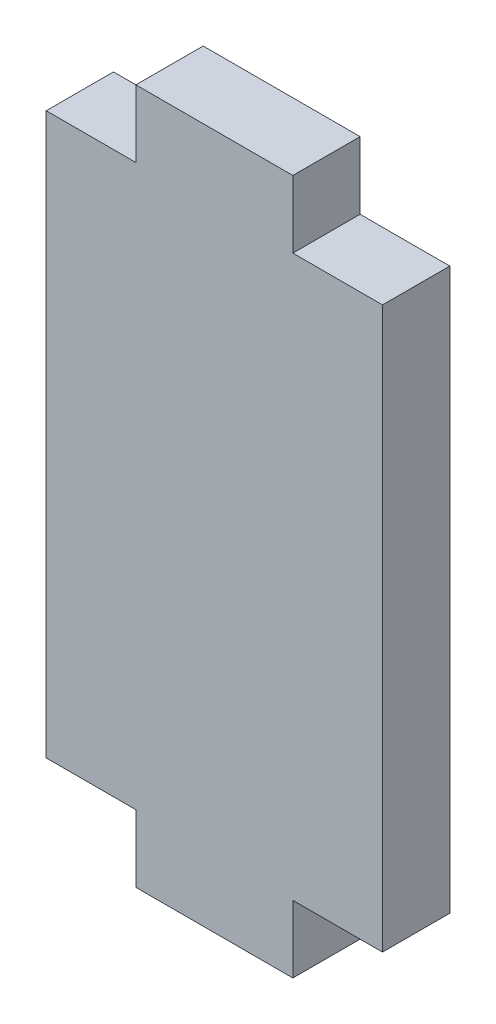
SolidWorks part; units mm, degrees
ref_plane "Front Plane" through (0, 0, 0) normal (0, 0, 1) x (1, 0, 0)
ref_plane "Top Plane" through (0, 0, 0) normal (0, 1, 0) x (1, 0, 0)
ref_plane "Right Plane" through (0, 0, 0) normal (1, 0, 0) x (0, 0, -1)
sketch "Sketch1" plane through (0, 0, 0) normal (0, 0, 1) x (1, 0, 0)
  line L0 (3.5, 12.5) -> (7.5, 12.5)
  line L1 (-7.5, 12.5) -> (-3.5, 12.5)
  line L2 (-7.5, 12.5) -> (-7.5, -12.5)
  line L3 (-7.5, -12.5) -> (-3.5, -12.5)
  line L4 (7.5, 12.5) -> (7.5, -12.5)
  line L5 (-7.5, 12.5) -> (7.5, -12.5) construction
  line L6 (-7.5, -12.5) -> (7.5, 12.5) construction
  line L8 (-3.5, -12.5) -> (-3.5, -15.5)
  line L9 (-3.5, -15.5) -> (3.5, -15.5)
  line L10 (3.5, -12.5) -> (3.5, -15.5)
  line L11 (3.5, -12.5) -> (7.5, -12.5)
  line L12 (-3.5, 12.5) -> (-3.5, 15.5)
  line L13 (-3.5, 15.5) -> (3.5, 15.5)
  line L14 (3.5, 12.5) -> (3.5, 15.5)
  point P0 (0, 0)
  dimension "D1" = 15
  dimension "D2" = 25
  dimension "D3" = 3
  dimension "D4" = 3
  dimension "D5" = 4
  dimension "D6" = 4
  dimension "D7" = 4
  dimension "D8" = 4
extrude "Boss-Extrude1" add sketch "Sketch1" along normal mid plane 3
